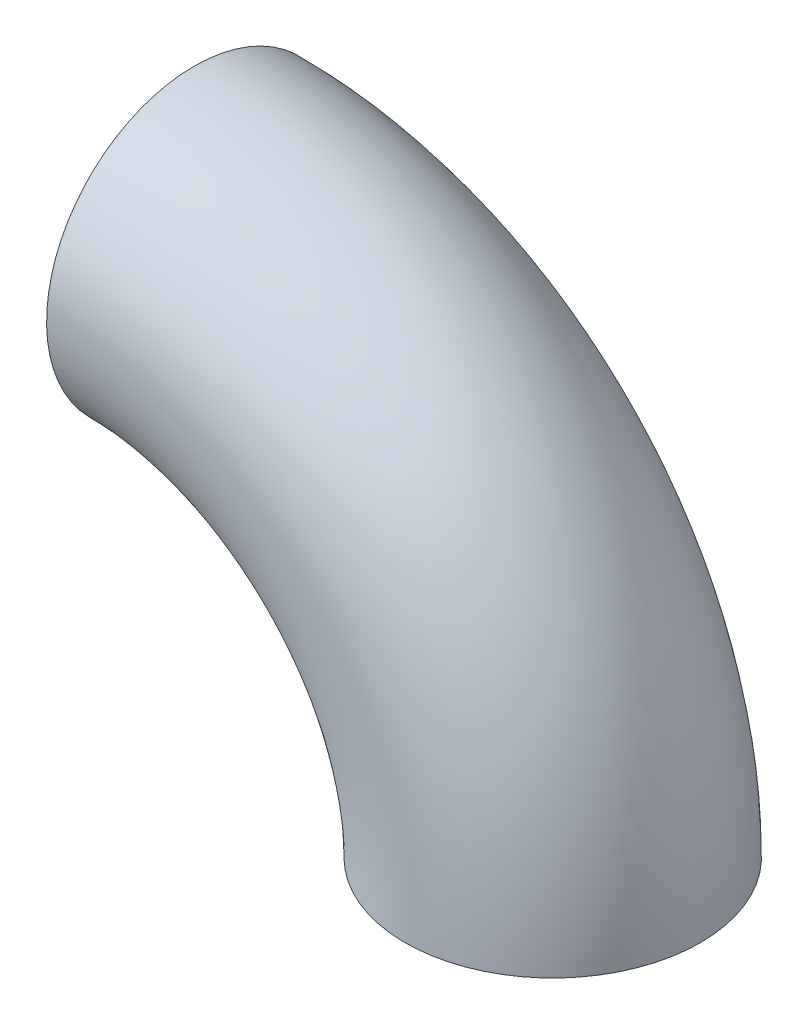
SolidWorks part; units mm, degrees
ref_plane "Front" through (0, 0, 0) normal (0, 0, 1) x (1, 0, 0)
ref_plane "Top" through (0, 0, 0) normal (0, 1, 0) x (1, 0, 0)
ref_plane "Right" through (0, 0, 0) normal (1, 0, 0) x (0, 0, -1)
sketch "Sketch1" plane through (0, 0, 0) normal (0, 1, 0) x (1, 0, 0)
  line L0 (0, 0) -> (22.225, 0) construction
  circle A0 centre (0, 0) radius 20.574
  circle A1 centre (0, 0) radius 22.225
  dimension "D1" = 1.651
sketch3d "3DSketch2"
  arc A0 (22.225, 0, 0) -> (-53.975, 76.2, 0) centre (-53.975, 0, 0) ccw
  point P4 (-53.975, 0, 76.2)
sweep "Sweep1" add profiles "Sketch1" path "3DSketch2"
